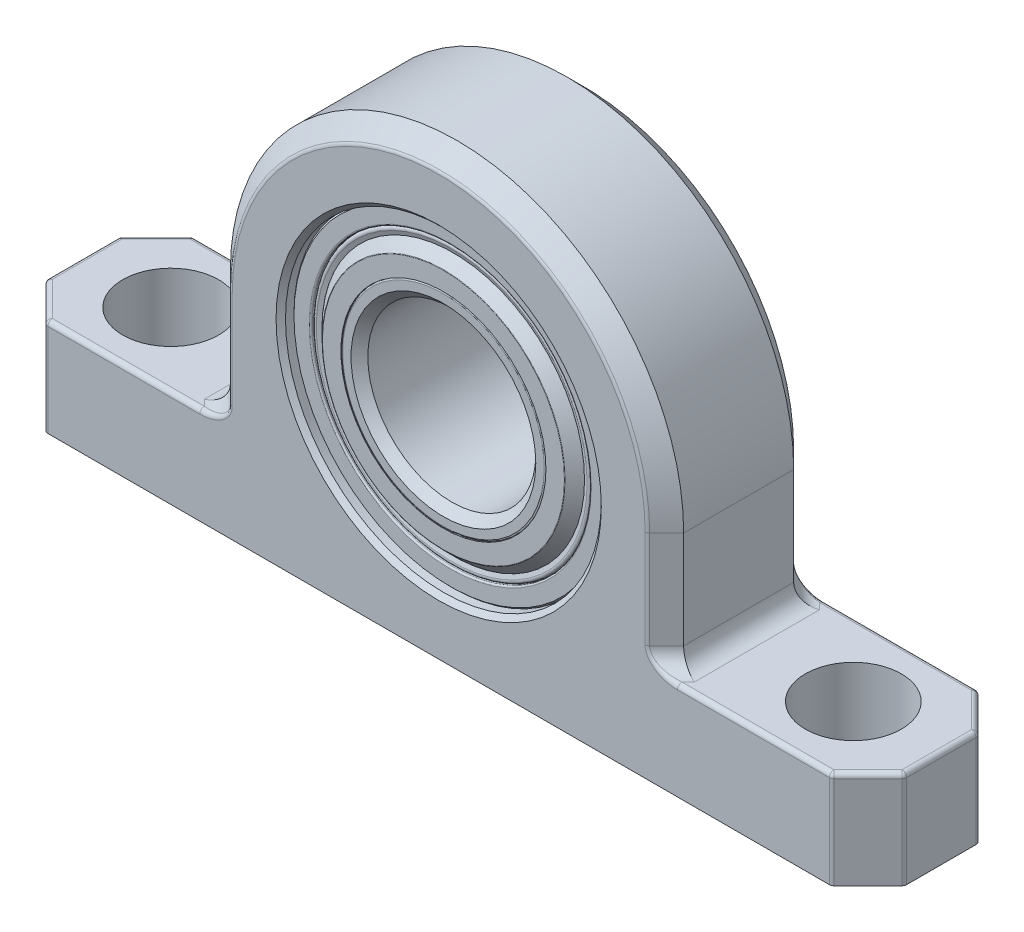
SolidWorks part; units mm, degrees
ref_plane "Front Plane" through (0, 0, 0) normal (0, 0, 1) x (1, 0, 0)
ref_plane "Top Plane" through (0, 0, 0) normal (0, 1, 0) x (1, 0, 0)
ref_plane "Right Plane" through (0, 0, 0) normal (1, 0, 0) x (0, 0, -1)
sketch "Sketch1" plane through (0, 0, 0) normal (0, 0, 1) x (1, 0, 0)
  line L0 (33.7344, 0) -> (33.7344, -17.272)
  line L1 (33.7344, -17.272) -> (63.8969, -17.272)
  line L2 (63.8969, -17.272) -> (63.8969, -31.75)
  line L3 (63.8969, -31.75) -> (-63.8969, -31.75)
  line L4 (-63.8969, -31.75) -> (-63.8969, -17.272)
  line L5 (-63.8969, -17.272) -> (-33.7344, -17.272)
  line L6 (-33.7344, -17.272) -> (-33.7344, 0)
  circle A0 centre (0, 0) radius 12.5
  arc A1 (33.7344, 0) -> (-33.7344, 0) centre (0, 0) ccw
  circle A2 centre (0, 0) radius 23.5
  point P12 (0, 23.5)
  point P13 (0, 12.5)
  dimension "ID" = 25
  dimension "Bearing OD" = 47
  dimension "Block OD" = 67.4688
  dimension "Collar Height" = 14.478
  dimension "Overall Length" = 127.7937
  dimension "Center Height" = 31.75
  dimension "Overall Height" = 65.4844
sketch "Sketch2" plane through (0, 0, 0) normal (0, 1, 0) x (1, 0, 0)
  line L0 (0, 10.9141) -> (0, -10.9141) construction
  line L1 (-50.8, 0) -> (50.8, 0) construction
  circle A0 centre (50.8, 0) radius 7.1437 construction
  circle A1 centre (-50.8, 0) radius 7.1437 construction
  dimension "Mounting Hole Diameter" = 14.2875
  dimension "Overall Width" = 21.8281
  dimension "Mounting Hole Center -to-Center" = 101.6
sketch "Sketch3" plane through (0, 0, 0) normal (0, 0, 1) x (1, 0, 0)
  line L0 (33.7344, 0) -> (33.7344, -17.272) construction
  line L1 (63.8969, -17.272) -> (63.8969, -31.75) construction
  line L2 (33.7344, -17.272) -> (63.8969, -17.272) construction
  line L3 (63.8969, -31.75) -> (-63.8969, -31.75) construction
  line L4 (-63.8969, -31.75) -> (-63.8969, -17.272) construction
  line L5 (-63.8969, -17.272) -> (-33.7344, -17.272) construction
  line L6 (-33.7344, -17.272) -> (-33.7344, 0) construction
  line L7 (33.7344, 0) -> (33.7344, -17.272)
  line L8 (63.8969, -17.272) -> (63.8969, -31.75)
  line L9 (33.7344, -17.272) -> (63.8969, -17.272)
  line L10 (63.8969, -31.75) -> (-63.8969, -31.75)
  line L11 (-63.8969, -31.75) -> (-63.8969, -17.272)
  line L12 (-63.8969, -17.272) -> (-33.7344, -17.272)
  line L13 (-33.7344, -17.272) -> (-33.7344, 0)
  arc A0 (33.7344, 0) -> (-33.7344, 0) centre (0, 0) ccw construction
  circle A1 centre (0, 0) radius 23.5 construction
  arc A2 (33.7344, 0) -> (-33.7344, 0) centre (0, 0) ccw
  circle A3 centre (0, 0) radius 23.5
extrude "Extrude1" add sketch "Sketch3" along normal up to vertex (10.9141 mm away) and the other way up to vertex (10.9141 mm away) up to point (0, 0, 10.9141) other way up to point (0, 0, -10.9141)
sketch "Sketch4" plane through (0, -17.272, 0) normal (0, 1, 0) x (1, 0, 0)
  line L0 (-63.8969, 10.9141) -> (-63.8969, 5.457)
  line L1 (-63.8969, -10.9141) -> (-63.8969, 10.9141) construction
  line L2 (-63.8969, 5.457) -> (-58.4398, 10.9141)
  line L3 (-33.7344, 10.9141) -> (-63.8969, 10.9141) construction
  line L4 (-58.4398, 10.9141) -> (-63.8969, 10.9141)
  line L5 (0, 0) -> (0, 10.9141) construction
  line L6 (0, 0) -> (-50.8, 0) construction
  line L7 (58.4398, 10.9141) -> (63.8969, 10.9141)
  line L8 (63.8969, 5.457) -> (58.4398, 10.9141)
  line L9 (63.8969, 10.9141) -> (63.8969, 5.457)
  line L10 (63.8969, -10.9141) -> (63.8969, -5.457)
  line L11 (63.8969, -5.457) -> (58.4398, -10.9141)
  line L12 (58.4398, -10.9141) -> (63.8969, -10.9141)
  line L13 (-58.4398, -10.9141) -> (-63.8969, -10.9141)
  line L14 (-63.8969, -5.457) -> (-58.4398, -10.9141)
  line L15 (-63.8969, -10.9141) -> (-63.8969, -5.457)
  circle A0 centre (-50.8, 0) radius 7.1437 construction
  circle A1 centre (50.8, 0) radius 7.1437 construction
  circle A2 centre (-50.8, 0) radius 7.1437
  circle A3 centre (50.8, 0) radius 7.1437
  dimension "D1" = 45
  dimension "D2" = 5.457
extrude "Cut-Extrude1" cut sketch "Sketch4" against normal through all
chamfer "Chamfer3" distance 2.7285 angle 45 6 edges at (-33.7344, -8.636, -10.9141) (0, 33.7344, -10.9141) (33.7344, -8.636, -10.9141) (-33.7344, -8.636, 10.9141) (0, 33.7344, 10.9141) (33.7344, -8.636, 10.9141)
fillet "Fillet6" radius 2.7285 6 edges at (33.7344, -17.272, 0) (32.3701, -17.272, -9.5498) (32.3701, -17.272, 9.5498) (-32.3701, -17.272, -9.5498) (-32.3701, -17.272, 9.5498) (-33.7344, -17.272, 0)
fillet "Fillet7" radius 0.6821 28 edges at (46.6522, -17.272, -10.9141) (32.136, -16.4728, -10.9141) (31.0059, -7.2717, -10.9141) (0, 31.0059, -10.9141) (-31.0059, -7.2717, -10.9141) (-32.136, -16.4728, -10.9141) (46.6522, -17.272, 10.9141) (32.136, -16.4728, 10.9141) (31.0059, -7.2717, 10.9141) (0, 31.0059, 10.9141) (-31.0059, -7.2717, 10.9141) (-32.136, -16.4728, 10.9141) (61.1684, -17.272, 8.1855) (63.8969, -17.272, 0) (61.1684, -17.272, -8.1855) (-46.6522, -17.272, -10.9141) (-61.1684, -17.272, -8.1855) (-63.8969, -17.272, 0) (-61.1684, -17.272, 8.1855) (-46.6522, -17.272, 10.9141) (-63.8969, -24.511, -5.457) (-58.4398, -24.511, -10.9141) (-63.8969, -24.511, 5.457) (-58.4398, -24.511, 10.9141) (58.4398, -24.511, -10.9141) (63.8969, -24.511, -5.457) (63.8969, -24.511, 5.457) (58.4398, -24.511, 10.9141)
chamfer "Chamfer4" distance 0.705 angle 45 2 edges at (23.5, 0, -10.9141) (23.5, 0, 10.9141)
sketch "Sketch5" plane through (0, 0, 0) normal (1, 0, 0) x (0, 0, -1)
  line L2 (9.1882, 23.5) -> (9.1882, 20.75)
  line L4 (9.1882, 20.75) -> (-9.1882, 20.75)
  line L5 (-10.2091, 23.5) -> (-10.2091, -23.5) construction
  line L8 (-10.2091, 12.5) -> (10.2091, 12.5)
  line L9 (10.2091, 15.25) -> (-10.2091, 15.25)
  line L10 (-9.1882, 23.5) -> (9.1882, 23.5)
  line L12 (-10.2091, 15.25) -> (-10.2091, 12.5)
  line L13 (-9.1882, 23.5) -> (-9.1882, 20.75)
  line L17 (0, 23.5) -> (0, 33.7344) construction
  line L18 (0, 33.7344) -> (0, 0) construction
  line L24 (10.2091, 15.25) -> (10.2091, 12.5)
  line L27 (8.1855, 33.7344) -> (-8.1855, 33.7344) construction
  dimension "D1" = 11
  dimension "D2" = 5.5
  dimension "D3" = 18.3763
  dimension "D4" = 20.4181
revolve "Revolve1" add sketch "Sketch5" angle 360 about L0
sketch "Sketch6" plane through (0, 0, 0) normal (1, 0, 0) x (0, 0, -1)
  line L0 (-10.2091, 15.2627) -> (-10.2091, 18)
  line L1 (-10.1719, 18.0898) -> (-8.2545, 20.0072)
  line L2 (-8.9466, 20.1606) -> (-8.7258, 19.5539)
  line L3 (-10.1837, 15.2627) -> (-10.1837, 18)
  line L4 (-10.1539, 18.0718) -> (-8.2365, 19.9892)
  line L5 (-8.9705, 20.1519) -> (-8.7496, 19.5452)
  line L6 (-10.2091, 15.2627) -> (-10.1837, 15.2627)
  line L7 (-8.7258, 19.5539) -> (-8.7496, 19.5452)
  line L8 (9.1882, 20.75) -> (-9.1882, 20.75) construction
  line L10 (0, 0) -> (0, 2.6695) construction
  line L11 (10.2091, 15.2627) -> (10.1837, 15.2627)
  line L12 (10.1837, 15.2627) -> (10.1837, 18)
  line L13 (10.1539, 18.0718) -> (8.2365, 19.9892)
  line L14 (8.9705, 20.1519) -> (8.7496, 19.5452)
  line L15 (8.7258, 19.5539) -> (8.7496, 19.5452)
  line L16 (8.9466, 20.1606) -> (8.7258, 19.5539)
  line L17 (10.1719, 18.0898) -> (8.2545, 20.0072)
  line L18 (10.2091, 15.2627) -> (10.2091, 18)
  line L19 (0, 0) -> (1.2184, 0) construction
  line L20 (-10.2091, 15.25) -> (-10.2091, 12.5) construction
  line L21 (-9.1882, 20.75) -> (-9.1882, 15.25) construction
  line L22 (10.2091, 15.25) -> (-10.2091, 15.25) construction
  arc A0 (-10.2091, 18) -> (-10.1719, 18.0898) centre (-10.0821, 18) cw
  arc A1 (-8.2545, 20.0072) -> (-8.9466, 20.1606) centre (-8.5517, 20.3043) ccw
  arc A2 (-10.1837, 18) -> (-10.1539, 18.0718) centre (-10.0821, 18) cw
  arc A3 (-8.2365, 19.9892) -> (-8.9705, 20.1519) centre (-8.5517, 20.3043) ccw
  arc A4 (10.1837, 18) -> (10.1539, 18.0718) centre (10.0821, 18) ccw
  arc A5 (8.2365, 19.9892) -> (8.9705, 20.1519) centre (8.5517, 20.3043) cw
  arc A6 (8.2545, 20.0072) -> (8.9466, 20.1606) centre (8.5517, 20.3043) cw
  arc A7 (10.2091, 18) -> (10.1719, 18.0898) centre (10.0821, 18) ccw
  point P2 (-9.1882, 18)
  dimension "D1" = 45
  dimension "D2" = 0.127
  dimension "D5" = 65
  dimension "D6" = 0.0127
  dimension "D4" = 0.0127
  dimension "D3" = 0.0254
revolve "Revolve2" add sketch "Sketch6" angle 360 about L19
chamfer "Chamfer5" distance 1.25 angle 45 2 edges at (-12.5, 0, 10.2091) (-12.5, 0, -10.2091)
fillet "Fillet8" radius 0.25 2 edges at (-15.25, 0, -10.2091) (-15.25, 0, 10.2091)
fillet "Fillet9" radius 0.235 2 edges at (-20.75, 0, -9.1882) (-20.75, 0, 9.1882)
chamfer "Chamfer6" distance 0.235 angle 45 2 edges at (-23.5, 0, -9.1882) (-23.5, 0, 9.1882)
equation "\"D2@Sketch4\" = \"Overall Width@Sketch2\" / 4"
equation "\"D1@Chamfer3\"=\"Overall Width@Sketch2\" / 8"
equation "\"D1@Fillet6\"=\"D1@Chamfer3\""
equation "\"D3@Sketch5\"=(\"Overall Width@Sketch2\"-2*\"D1@Chamfer4\")*.9"
equation "\"D2@Sketch6\"=\"D3@Sketch6\"*5"
equation "\"D1@Chamfer5\"=\"ID@Sketch1\"*.05"
equation "\"D1@Fillet8\"=\"ID@Sketch1\"*.01"
equation "\"D1@Fillet9\"=\"Bearing OD@Sketch1\"*.005"
equation "\"D1@Chamfer6\"=\"Bearing OD@Sketch1\"*.005"
equation "\"D1@Chamfer4\"=\"Bearing OD@Sketch1\"*.015"
equation "\"D1@Fillet7\"=\"Overall Width@Sketch2\"*.03125"
equation "\"D2@Sketch5\"=(\"Bearing OD@Sketch1\"-\"ID@Sketch1\")/2*.5"
